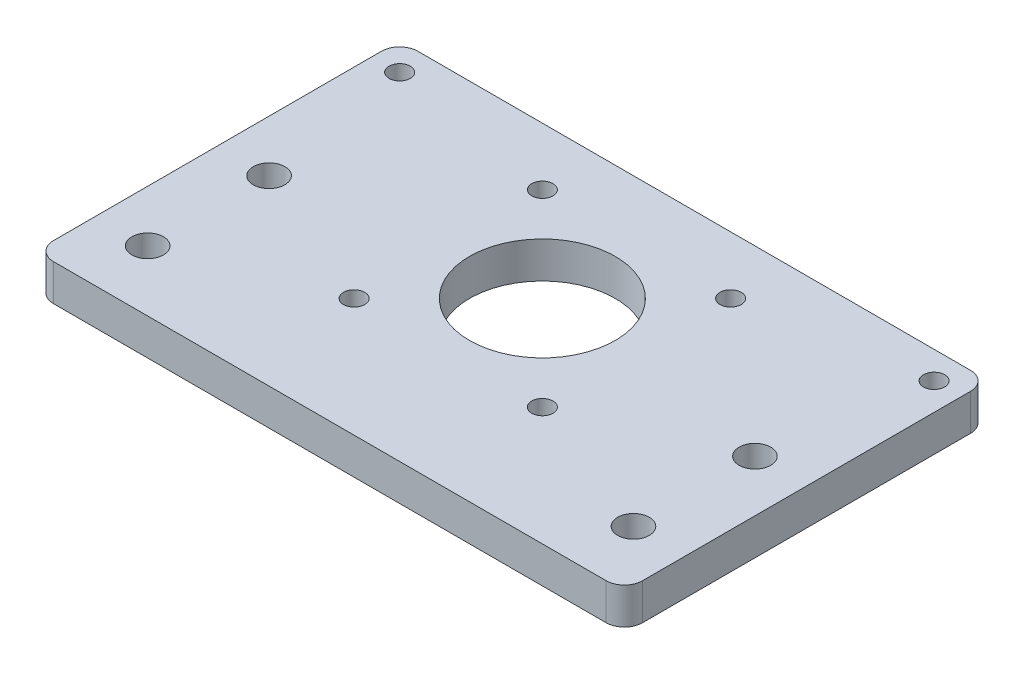
SolidWorks part; units mm, degrees
material "Polycarbonate (PC)"
ref_plane "Front Plane" through (0, 0, 0) normal (0, 0, 1) x (1, 0, 0)
ref_plane "Top Plane" through (0, 0, 0) normal (0, 1, 0) x (1, 0, 0)
ref_plane "Right Plane" through (0, 0, 0) normal (1, 0, 0) x (0, 0, -1)
sketch "Sketch1" plane through (0, 0, 0) normal (0, 1, 0) x (1, 0, 0)
  line L1 (48.5, -30) -> (-48.5, -30)
  line L2 (48.5, -30) -> (48.5, 30)
  line L3 (48.5, 30) -> (-48.5, 30)
  line L4 (-48.5, -30) -> (-48.5, 30)
  line L5 (48.5, -30) -> (-48.5, 30) construction
  line L6 (48.5, 30) -> (-48.5, -30) construction
  point P0 (0, 0)
  dimension "D1" = 97
  dimension "D2" = 60
extrude "Base" add sketch "Sketch1" along normal blind 6
sketch "Sketch2" plane through (0, 6, 0) normal (0, 1, 0) x (1, 0, 0)
  line L1 (0, 5) -> (0, 17.5) construction
  line L2 (-48.5, -30) -> (48.5, -30) construction
  circle A2 centre (0, 5) radius 12
  dimension "D1" = 24
  dimension "D2" = 35
extrude "StepperCaseHole" cut sketch "Sketch2" against normal through all
fillet "FilletEdges3mm" radius 3 4 edges at (48.5, 3, 30) (48.5, 3, -30) (-48.5, 3, -30) (-48.5, 3, 30)
hole_wizard "Ø3.5mm CableTieHoles" positions "Sketch6" profile "Sketch7" hole size "Ø3.5" standard "ISO" end condition through all
sketch "Sketch6" plane through (0, 0, 0) normal (0, -1, 0) x (-1, 0, 0)
  line L0 (-45.5, 30) -> (45.5, 30) construction
  line L1 (-48.5, -27) -> (-48.5, 27) construction
  line L2 (48.5, 27) -> (48.5, -27) construction
  point P0 (-44, 25.5)
  point P2 (44, 25.5)
  dimension "D1" = 4.5
  dimension "D2" = 4.5
  dimension "D3" = 4.5
sketch "Sketch7" plane through (44, 0, -25.5) normal (1, 0, 0) x (0, 0, -1)
  line L0 (0, 0) -> (0, 6)
  line L1 (0, 6) -> (1.75, 6)
  line L2 (1.75, 6) -> (1.75, 0)
  line L5 (1.75, 0) -> (0, 0)
  line L11 (0, -6.35) -> (0, 107.95) construction
  dimension "Thru Hole Dia." = 3.5
  dimension "Thru Hole Depth" = 6
hole_wizard "Ø5.2 (5.2) HolesForCorners" positions "Sketch8" profile "Sketch9" hole size "Ø5.2" standard "ISO" end condition through all
sketch "Sketch8" plane through (0, 6, 0) normal (0, 1, 0) x (1, 0, 0)
  line L0 (0, 0) -> (0, 10.0505) construction
  line L2 (-45.5, -30) -> (45.5, -30) construction
  point P0 (-40, 0)
  point P2 (-40, -20)
  point P4 (40, 0)
  point P6 (40, -20)
  dimension "D1" = 80
  dimension "D2" = 20
  dimension "D3" = 10
sketch "Sketch9" plane through (-40, 6, 0) normal (1, 0, 0) x (0, 0, 1)
  line L0 (0, 0) -> (0, 6)
  line L1 (0, 6) -> (2.6, 6)
  line L2 (2.6, 6) -> (2.6, 0)
  line L5 (2.6, 0) -> (0, 0)
  line L11 (0, -6.35) -> (0, 107.95) construction
  dimension "Thru Hole Dia." = 5.2
  dimension "Thru Hole Depth" = 6
hole_wizard "Ø3.5 (3.5) StepperMountHoles" positions "Sketch10" profile "Sketch11" hole size "Ø3.5" standard "ISO" end condition through all
sketch "Sketch10" plane through (0, 6, 0) normal (0, 1, 0) x (1, 0, 0)
  line L2 (0, 12.5358) -> (0, 5) construction
  line L3 (-45.5, -30) -> (45.5, -30) construction
  point P0 (-15.5, 20.5)
  point P2 (-15.5, -10.5)
  point P4 (15.5, -10.5)
  point P6 (15.5, 20.5)
  dimension "D1" = 31
  dimension "D2" = 31
  dimension "D3" = 19.5
sketch "Sketch11" plane through (-15.5, 6, -20.5) normal (1, 0, 0) x (0, 0, 1)
  line L0 (0, 0) -> (0, 6)
  line L1 (0, 6) -> (1.75, 6)
  line L2 (1.75, 6) -> (1.75, 0)
  line L5 (1.75, 0) -> (0, 0)
  line L11 (0, -6.35) -> (0, 107.95) construction
  dimension "Thru Hole Dia." = 3.5
  dimension "Thru Hole Depth" = 6
